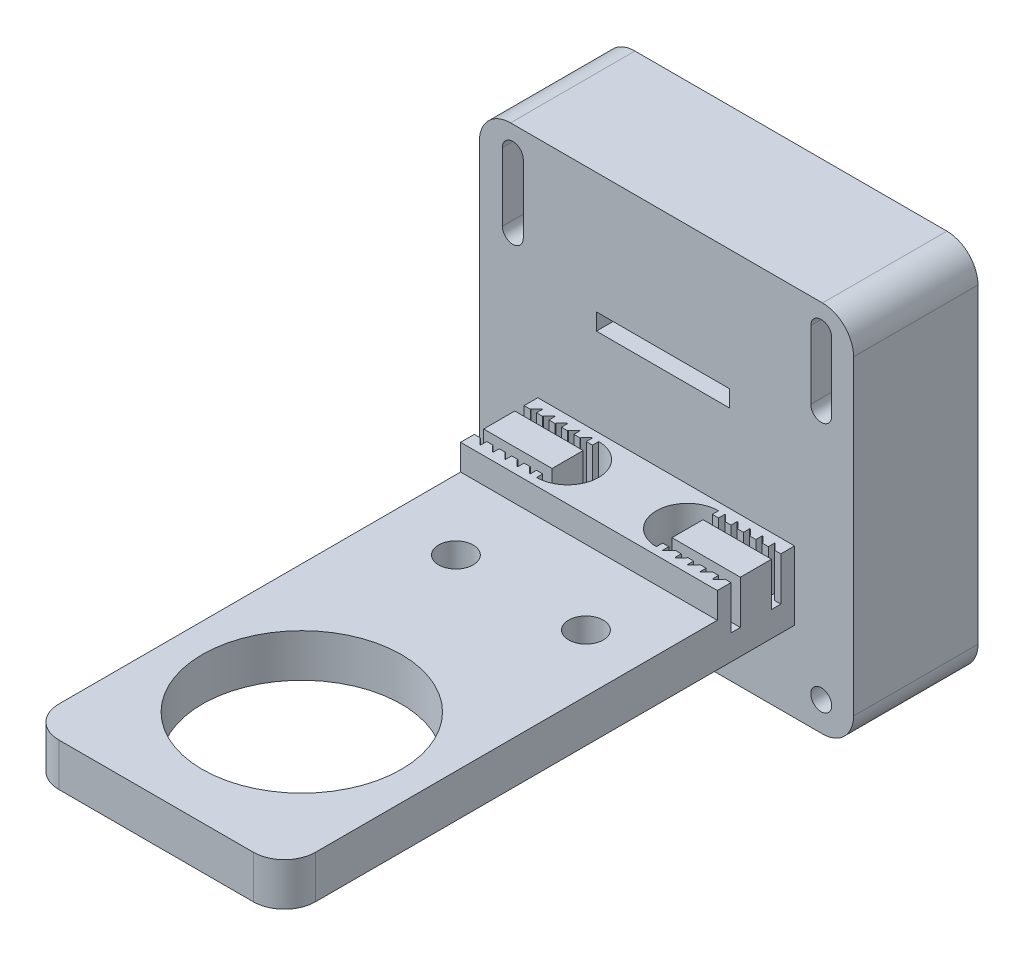
SolidWorks part; units mm, degrees
ref_plane "Alzado" through (0, 0, 0) normal (0, 0, 1) x (1, 0, 0)
ref_plane "Planta" through (0, 0, 0) normal (0, 1, 0) x (1, 0, 0)
ref_plane "Vista lateral" through (0, 0, 0) normal (1, 0, 0) x (0, 0, -1)
sketch "Croquis1" plane through (0, 0, 0) normal (0, 0, 1) x (1, 0, 0)
  line L0 (-21.7038, 24.1707) -> (-21.7038, 13.2033) construction
  line L1 (-27.0724, 28.25) -> (33.0729, 28.25)
  line L2 (-27.0724, 28.25) -> (-27.0724, -31.75)
  line L3 (-27.0724, -31.75) -> (33.0729, -31.75)
  line L4 (33.0729, 28.25) -> (33.0729, -31.75)
  line L5 (-8.2743, 8.8387) -> (13.1009, 8.8387)
  line L6 (-8.2743, 8.8387) -> (-8.2743, 6.1528)
  line L7 (-8.2743, 6.1528) -> (13.1009, 6.1528)
  line L8 (13.1009, 8.8387) -> (13.1009, 6.1528)
  line L9 (-20.0251, 24.1707) -> (-20.0251, 13.2033)
  line L10 (-23.3825, 24.1707) -> (-23.3825, 13.2033)
  line L11 (27.8733, 24.1707) -> (27.8733, 13.2033) construction
  line L12 (29.552, 24.1707) -> (29.552, 13.2033)
  line L13 (26.1946, 24.1707) -> (26.1946, 13.2033)
  circle A2 centre (27.8733, -27.0851) radius 1.6787
  circle A3 centre (-21.7038, -27.0851) radius 1.6787
  arc A4 (-20.0251, 24.1707) -> (-23.3825, 24.1707) centre (-21.7038, 24.1707) ccw
  arc A5 (-23.3825, 13.2033) -> (-20.0251, 13.2033) centre (-21.7038, 13.2033) ccw
  arc A6 (29.552, 24.1707) -> (26.1946, 24.1707) centre (27.8733, 24.1707) ccw
  arc A7 (26.1946, 13.2033) -> (29.552, 13.2033) centre (27.8733, 13.2033) ccw
  point P16 (-21.7038, 18.687)
  point P22 (27.8733, 18.687)
  dimension "D1" = 60.1453
  dimension "D2" = 60
extrude "Saliente-Extruir1" add sketch "Croquis1" along normal blind 20
sketch "Croquis2" plane through (0, 0, 20) normal (0, 0, 1) x (1, 0, 0)
  line L1 (-17.6867, -7.8196) -> (23.5792, -7.8196)
  line L2 (-17.6867, -7.8196) -> (-17.6867, -18.8667)
  line L3 (-17.6867, -18.8667) -> (23.5792, -18.8667)
  line L4 (23.5792, -7.8196) -> (23.5792, -18.8667)
extrude "Saliente-Extruir2" add sketch "Croquis2" along normal blind 82
sketch "Croquis3" plane through (23.5792, 0, 0) normal (1, 0, 0) x (0, 0, -1)
  line L1 (-54.9335, -4.4205) -> (-32.4143, -4.4205)
  line L2 (-54.9335, -4.4205) -> (-54.9335, -11.9623)
  line L3 (-54.9335, -11.9623) -> (-32.4143, -11.9623)
  line L4 (-32.4143, -11.9623) -> (-32.4143, -4.4205)
extrude "Cortar-Extruir1" cut sketch "Croquis3" against normal blind 50
sketch "Croquis4" plane through (0, -18.8667, 0) normal (0, -1, 0) x (1, 0, 0)
  circle A0 centre (-6.5237, 44.3331) radius 2.7788
  circle A1 centre (14.3869, 44.3331) radius 2.7788
extrude "Cortar-Extruir2" cut sketch "Croquis4" against normal blind 52
fillet "Redondeo1" radius 5 2 edges at (-17.6867, -13.3431, 102) (23.5792, -13.3431, 102)
fillet "Redondeo2" radius 5 4 edges at (-27.0724, 28.25, 10) (33.0729, 28.25, 10) (-27.0724, -31.75, 10) (33.0729, -31.75, 10)
sketch "Croquis5" plane through (0, -7.8196, 0) normal (0, 1, 0) x (1, 0, 0)
  circle A2 centre (2.9463, -78.5735) radius 16
extrude "Cortar-Extruir3" cut sketch "Croquis5" against normal blind 20
sketch "Croquis7" plane through (-17.6867, 0, 0) normal (-1, 0, 0) x (0, 0, 1)
  line L1 (54.9335, -7.8196) -> (107.4711, -7.8196)
  line L2 (54.9335, -7.8196) -> (54.9335, -11.9623)
  line L3 (54.9335, -11.9623) -> (107.4711, -11.9623)
  line L4 (107.4711, -7.8196) -> (107.4711, -11.9623)
extrude "Cortar-Extruir4" cut sketch "Croquis7" against normal blind 62
sketch "Croquis8" plane through (0, -7.8196, 0) normal (0, 1, 0) x (1, 0, 0)
  line L0 (-17.6867, -26.2072) -> (-6.6867, -26.2072) construction
  line L1 (-8.6867, -30.3072) -> (-7.7867, -31.2072)
  line L3 (-17.6867, -22.2072) -> (-6.6867, -22.2072) construction
  line L5 (-17.6867, -32.4143) -> (-17.6867, -20) construction
  line L6 (-13.6867, -22.2072) -> (-12.6867, -22.2072)
  line L7 (-17.6867, -22.2072) -> (-16.6867, -22.2072)
  line L8 (-11.6867, -22.2072) -> (-10.6867, -22.2072)
  line L9 (-17.6867, -23.7072) -> (-6.6867, -23.7072)
  line L10 (-17.6867, -22.2072) -> (-16.6867, -22.2072)
  line L11 (-9.6867, -22.2072) -> (-8.6867, -22.2072)
  line L12 (-7.6867, -22.2072) -> (-6.6867, -22.2072)
  line L13 (-16.6867, -22.2072) -> (-16.6867, -22.1072)
  line L14 (-15.7867, -21.2072) -> (-15.6867, -21.2072)
  line L15 (-15.6867, -21.2072) -> (-15.6867, -22.2072)
  line L16 (-16.6867, -22.1072) -> (-15.7867, -21.2072)
  line L17 (-15.6867, -22.2072) -> (-14.6867, -22.2072)
  line L18 (-15.6867, -22.2072) -> (-14.6867, -22.2072)
  line L19 (-15.6867, -22.2072) -> (-14.6867, -22.2072)
  line L20 (-14.6867, -22.2072) -> (-14.6867, -22.1072)
  line L21 (-13.7867, -21.2072) -> (-13.6867, -21.2072)
  line L22 (-13.6867, -21.2072) -> (-13.6867, -22.2072)
  line L23 (-14.6867, -22.1072) -> (-13.7867, -21.2072)
  line L24 (-13.6867, -22.2072) -> (-12.6867, -22.2072)
  line L25 (-13.6867, -22.2072) -> (-12.6867, -22.2072)
  line L26 (-12.6867, -22.2072) -> (-12.6867, -22.1072)
  line L27 (-11.7867, -21.2072) -> (-11.6867, -21.2072)
  line L28 (-11.6867, -21.2072) -> (-11.6867, -22.2072)
  line L29 (-12.6867, -22.1072) -> (-11.7867, -21.2072)
  line L30 (-11.6867, -22.2072) -> (-10.6867, -22.2072)
  line L31 (-11.6867, -22.2072) -> (-10.6867, -22.2072)
  line L32 (-10.6867, -22.2072) -> (-10.6867, -22.1072)
  line L33 (-9.7867, -21.2072) -> (-9.6867, -21.2072)
  line L34 (-9.6867, -21.2072) -> (-9.6867, -22.2072)
  line L35 (-10.6867, -22.1072) -> (-9.7867, -21.2072)
  line L36 (-9.6867, -22.2072) -> (-8.6867, -22.2072)
  line L37 (-9.6867, -22.2072) -> (-8.6867, -22.2072)
  line L38 (-8.6867, -22.2072) -> (-8.6867, -22.1072)
  line L39 (-7.7867, -21.2072) -> (-7.6867, -21.2072)
  line L40 (-7.6867, -21.2072) -> (-7.6867, -22.2072)
  line L41 (-8.6867, -22.1072) -> (-7.7867, -21.2072)
  line L42 (-17.6867, -28.7072) -> (-6.6867, -28.7072) construction
  line L43 (-17.6867, -30.2072) -> (-6.6867, -30.2072) construction
  line L44 (-7.6867, -31.2072) -> (-7.6867, -30.2072)
  line L45 (-7.7867, -31.2072) -> (-7.6867, -31.2072)
  line L46 (-8.6867, -30.2072) -> (-8.6867, -30.3072)
  line L47 (-9.6867, -30.2072) -> (-8.6867, -30.2072)
  line L48 (-9.6867, -30.2072) -> (-8.6867, -30.2072)
  line L49 (-10.6867, -30.3072) -> (-9.7867, -31.2072)
  line L50 (-9.6867, -31.2072) -> (-9.6867, -30.2072)
  line L51 (-9.7867, -31.2072) -> (-9.6867, -31.2072)
  line L52 (-10.6867, -30.2072) -> (-10.6867, -30.3072)
  line L53 (-11.6867, -30.2072) -> (-10.6867, -30.2072)
  line L54 (-11.6867, -30.2072) -> (-10.6867, -30.2072)
  line L55 (-12.6867, -30.3072) -> (-11.7867, -31.2072)
  line L56 (-11.6867, -31.2072) -> (-11.6867, -30.2072)
  line L57 (-11.7867, -31.2072) -> (-11.6867, -31.2072)
  line L58 (-12.6867, -30.2072) -> (-12.6867, -30.3072)
  line L59 (-13.6867, -30.2072) -> (-12.6867, -30.2072)
  line L60 (-13.6867, -30.2072) -> (-12.6867, -30.2072)
  line L61 (-14.6867, -30.3072) -> (-13.7867, -31.2072)
  line L62 (-13.6867, -31.2072) -> (-13.6867, -30.2072)
  line L63 (-13.7867, -31.2072) -> (-13.6867, -31.2072)
  line L64 (-14.6867, -30.2072) -> (-14.6867, -30.3072)
  line L65 (-15.6867, -30.2072) -> (-14.6867, -30.2072)
  line L66 (-15.6867, -30.2072) -> (-14.6867, -30.2072)
  line L67 (-15.6867, -30.2072) -> (-14.6867, -30.2072)
  line L68 (-16.6867, -30.3072) -> (-15.7867, -31.2072)
  line L69 (-15.6867, -31.2072) -> (-15.6867, -30.2072)
  line L70 (-15.7867, -31.2072) -> (-15.6867, -31.2072)
  line L71 (-16.6867, -30.2072) -> (-16.6867, -30.3072)
  line L72 (-7.6867, -30.2072) -> (-6.6867, -30.2072)
  line L73 (-9.6867, -30.2072) -> (-8.6867, -30.2072)
  line L74 (-17.6867, -30.2072) -> (-16.6867, -30.2072)
  line L75 (-17.6867, -28.7072) -> (-6.6867, -28.7072)
  line L76 (-11.6867, -30.2072) -> (-10.6867, -30.2072)
  line L77 (-17.6867, -30.2072) -> (-16.6867, -30.2072)
  line L78 (-13.6867, -30.2072) -> (-12.6867, -30.2072)
  line L79 (-6.6867, -21.2072) -> (-6.6867, -22.2072)
  line L80 (-6.6867, -30.2072) -> (-6.6867, -31.2072)
  line L81 (2.9463, -20) -> (2.9463, -32.4143)
  line L82 (23.5792, -20) -> (-17.6867, -20) construction
  line L83 (-17.6867, -32.4143) -> (23.5792, -32.4143) construction
  line L84 (12.5792, -30.2072) -> (12.5792, -31.2072)
  line L85 (12.5792, -21.2072) -> (12.5792, -22.2072)
  line L86 (19.5792, -30.2072) -> (18.5792, -30.2072)
  line L87 (23.5792, -30.2072) -> (22.5792, -30.2072)
  line L88 (17.5792, -30.2072) -> (16.5792, -30.2072)
  line L89 (23.5792, -28.7072) -> (12.5792, -28.7072)
  line L90 (23.5792, -30.2072) -> (22.5792, -30.2072)
  line L91 (15.5792, -30.2072) -> (14.5792, -30.2072)
  line L92 (13.5792, -30.2072) -> (12.5792, -30.2072)
  line L93 (22.5792, -30.2072) -> (22.5792, -30.3072)
  line L94 (21.6792, -31.2072) -> (21.5792, -31.2072)
  line L95 (21.5792, -31.2072) -> (21.5792, -30.2072)
  line L96 (22.5792, -30.3072) -> (21.6792, -31.2072)
  line L97 (21.5792, -30.2072) -> (20.5792, -30.2072)
  line L98 (21.5792, -30.2072) -> (20.5792, -30.2072)
  line L99 (21.5792, -30.2072) -> (20.5792, -30.2072)
  line L100 (20.5792, -30.2072) -> (20.5792, -30.3072)
  line L101 (19.6792, -31.2072) -> (19.5792, -31.2072)
  line L102 (19.5792, -31.2072) -> (19.5792, -30.2072)
  line L103 (20.5792, -30.3072) -> (19.6792, -31.2072)
  line L104 (19.5792, -30.2072) -> (18.5792, -30.2072)
  line L105 (19.5792, -30.2072) -> (18.5792, -30.2072)
  line L106 (18.5792, -30.2072) -> (18.5792, -30.3072)
  line L107 (17.6792, -31.2072) -> (17.5792, -31.2072)
  line L108 (17.5792, -31.2072) -> (17.5792, -30.2072)
  line L109 (18.5792, -30.3072) -> (17.6792, -31.2072)
  line L110 (17.5792, -30.2072) -> (16.5792, -30.2072)
  line L111 (17.5792, -30.2072) -> (16.5792, -30.2072)
  line L112 (16.5792, -30.2072) -> (16.5792, -30.3072)
  line L113 (15.6792, -31.2072) -> (15.5792, -31.2072)
  line L114 (15.5792, -31.2072) -> (15.5792, -30.2072)
  line L115 (16.5792, -30.3072) -> (15.6792, -31.2072)
  line L116 (15.5792, -30.2072) -> (14.5792, -30.2072)
  line L117 (15.5792, -30.2072) -> (14.5792, -30.2072)
  line L118 (14.5792, -30.2072) -> (14.5792, -30.3072)
  line L119 (13.6792, -31.2072) -> (13.5792, -31.2072)
  line L120 (13.5792, -31.2072) -> (13.5792, -30.2072)
  line L121 (14.5792, -22.1072) -> (13.6792, -21.2072)
  line L122 (13.5792, -21.2072) -> (13.5792, -22.2072)
  line L123 (13.6792, -21.2072) -> (13.5792, -21.2072)
  line L124 (14.5792, -22.2072) -> (14.5792, -22.1072)
  line L125 (15.5792, -22.2072) -> (14.5792, -22.2072)
  line L126 (15.5792, -22.2072) -> (14.5792, -22.2072)
  line L127 (16.5792, -22.1072) -> (15.6792, -21.2072)
  line L128 (15.5792, -21.2072) -> (15.5792, -22.2072)
  line L129 (15.6792, -21.2072) -> (15.5792, -21.2072)
  line L130 (16.5792, -22.2072) -> (16.5792, -22.1072)
  line L131 (17.5792, -22.2072) -> (16.5792, -22.2072)
  line L132 (17.5792, -22.2072) -> (16.5792, -22.2072)
  line L133 (18.5792, -22.1072) -> (17.6792, -21.2072)
  line L134 (17.5792, -21.2072) -> (17.5792, -22.2072)
  line L135 (17.6792, -21.2072) -> (17.5792, -21.2072)
  line L136 (18.5792, -22.2072) -> (18.5792, -22.1072)
  line L137 (19.5792, -22.2072) -> (18.5792, -22.2072)
  line L138 (19.5792, -22.2072) -> (18.5792, -22.2072)
  line L139 (20.5792, -22.1072) -> (19.6792, -21.2072)
  line L140 (19.5792, -21.2072) -> (19.5792, -22.2072)
  line L141 (19.6792, -21.2072) -> (19.5792, -21.2072)
  line L142 (20.5792, -22.2072) -> (20.5792, -22.1072)
  line L143 (21.5792, -22.2072) -> (20.5792, -22.2072)
  line L144 (21.5792, -22.2072) -> (20.5792, -22.2072)
  line L145 (21.5792, -22.2072) -> (20.5792, -22.2072)
  line L146 (22.5792, -22.1072) -> (21.6792, -21.2072)
  line L147 (21.5792, -21.2072) -> (21.5792, -22.2072)
  line L148 (21.6792, -21.2072) -> (21.5792, -21.2072)
  line L149 (22.5792, -22.2072) -> (22.5792, -22.1072)
  line L150 (13.5792, -22.2072) -> (12.5792, -22.2072)
  line L151 (15.5792, -22.2072) -> (14.5792, -22.2072)
  line L152 (23.5792, -22.2072) -> (22.5792, -22.2072)
  line L153 (23.5792, -23.7072) -> (12.5792, -23.7072)
  line L154 (17.5792, -22.2072) -> (16.5792, -22.2072)
  line L155 (23.5792, -22.2072) -> (22.5792, -22.2072)
  line L156 (19.5792, -22.2072) -> (18.5792, -22.2072)
  line L157 (14.5792, -30.3072) -> (13.6792, -31.2072)
  line L158 (-6.6867, -23.7072) -> (-6.6867, -28.7072)
  line L159 (-6.6867, -28.7072) -> (-6.8274, -28.7462)
  line L160 (-4.1867, -26.2072) -> (2.9508, -26.2072) construction
  line L161 (12.5792, -23.7072) -> (12.5792, -28.7072)
  arc A1 (-6.6867, -21.2072) -> (-6.6867, -31.2072) centre (-6.6867, -26.2072) cw
  arc A2 (12.5792, -21.2072) -> (12.5792, -31.2072) centre (12.5792, -26.2072) ccw
  arc A3 (-6.6867, -22.2072) -> (-6.6867, -30.2072) centre (-6.6867, -26.2072) cw construction
  arc A4 (-6.6867, -23.7072) -> (-6.6867, -28.7072) centre (-6.6867, -26.2072) cw construction
  point P28 (-16.6867, -21.2072)
  point P37 (-14.6867, -21.2072)
  point P44 (-12.6867, -21.2072)
  point P51 (-10.6867, -21.2072)
  point P58 (-8.6867, -21.2072)
  point P78 (-8.6867, -31.2072)
  point P79 (-10.6867, -31.2072)
  point P80 (-12.6867, -31.2072)
  point P81 (-14.6867, -31.2072)
  point P82 (-16.6867, -31.2072)
  point P96 (22.5792, -31.2072)
  point P155 (20.5792, -31.2072)
  point P156 (18.5792, -31.2072)
  point P157 (16.5792, -31.2072)
  point P158 (14.5792, -31.2072)
  point P159 (14.5792, -21.2072)
  point P160 (16.5792, -21.2072)
  point P161 (18.5792, -21.2072)
  point P162 (20.5792, -21.2072)
  point P163 (22.5792, -21.2072)
  dimension "D2" = 1
  dimension "D3" = 1.5
  dimension "D4" = 1
  dimension "D5" = 1
  dimension "D6" = 5
extrude "Cortar-Extruir5" cut sketch "Croquis8" against normal blind 7
